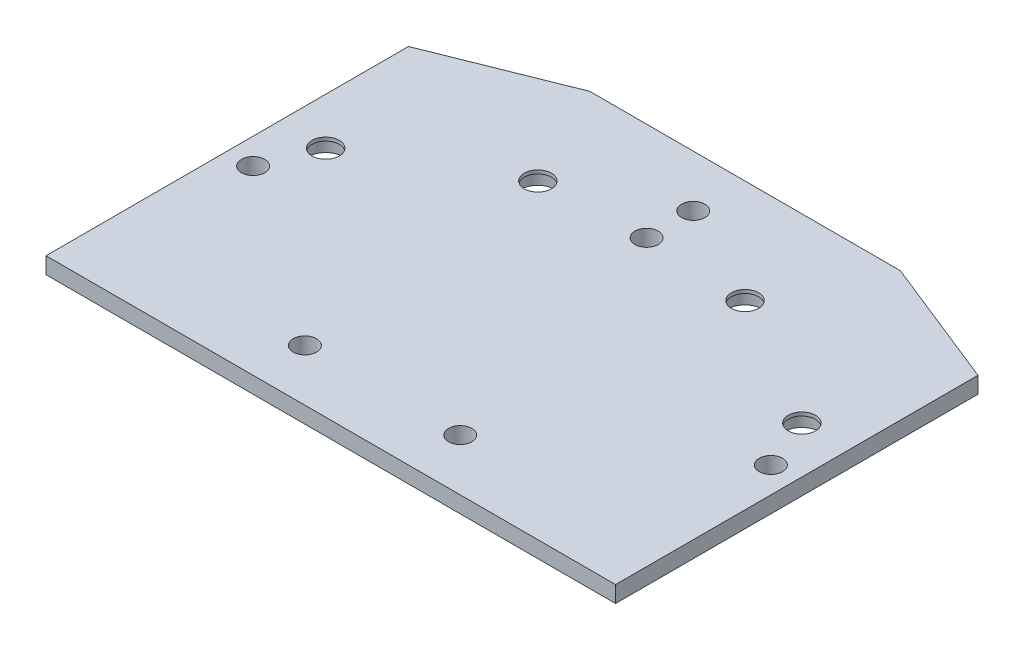
SolidWorks part; units mm, degrees
material "6061-T6 (SS)"
ref_plane "Front Plane" through (0, 0, 0) normal (0, 0, 1) x (1, 0, 0)
ref_plane "Top Plane" through (0, 0, 0) normal (0, 1, 0) x (1, 0, 0)
ref_plane "Right Plane" through (0, 0, 0) normal (1, 0, 0) x (0, 0, -1)
sketch "Sketch1" plane through (0, 0, 0) normal (0, 1, 0) x (1, 0, 0)
  line L0 (-55, 15) -> (-30, 25)
  line L1 (55, -55) -> (-55, -55)
  line L7 (30, 25) -> (55, 15)
  line L8 (-55, -55) -> (-55, 15)
  line L9 (55, -55) -> (55, 15)
  line L10 (30, 25) -> (-30, 25)
  point P0 (0, 0)
  dimension "D1" = 25
  dimension "D2" = 10
  dimension "D3" = 25
  dimension "D4" = 110
  dimension "D5" = 70
  dimension "D6" = 15
  dimension "D7" = 55
extrude "Boss-Extrude1" add sketch "Sketch1" along normal mid plane 3.175 contours L0 L10 L7 L9 L1 L8
sketch "Sketch4" plane through (0, 1.5875, 0) normal (0, 1, 0) x (1, 0, 0)
  line L0 (30, 25) -> (-30, 25) construction
  line L3 (-45.9808, -10) -> (-20, 5)
  line L5 (-55, -55) -> (-55, 15) construction
  point P0 (-20, 5)
  point P2 (20, 5)
  point P4 (45.9808, -10)
  point P6 (-45.9808, -10)
  dimension "D1" = 20
  dimension "D2" = 30
  dimension "D3" = 20
  dimension "D4" = 20
  dimension "D5" = 30
  dimension "D7" = 60
hole_wizard "Ø1.0mm Dowel Hole1" positions "Sketch4" profile "Sketch3" hole size "Ø1.0" standard "ANSI Metric" end condition through all
sketch "Sketch3" plane through (-20, 1.5875, -5) normal (1, 0, 0) x (0, 0, 1)
  line L0 (0, 0) -> (0, 3.175)
  line L1 (0, 3.175) -> (2.625, 3.175)
  line L2 (2.625, 3.175) -> (2.625, 0)
  line L5 (2.625, 0) -> (0, 0)
  line L11 (0, -6.35) -> (0, 107.95) construction
  dimension "Thru Hole Dia." = 5.25
  dimension "Thru Hole Depth" = 3.175
sketch "Sketch6" plane through (0, -1.5875, 0) normal (0, -1, 0) x (1, 0, 0)
  circle A0 centre (-45.9808, 10) radius 3.45
  circle A1 centre (-20, -5) radius 3.45
  circle A2 centre (20, -5) radius 3.45
  circle A3 centre (45.9808, 10) radius 3.45
  dimension "D1" = 6.9
  dimension "D2" = 6.9
  dimension "D3" = 6.9
  dimension "D4" = 6.9
extrude "Cut-Extrude2" cut sketch "Sketch6" against normal blind 2.5
sketch "Sketch9" plane through (0, -1.5875, 0) normal (0, -1, 0) x (-1, 0, 0)
  line L0 (-30, 25) -> (30, 25) construction
  point P0 (0, 15)
  point P2 (0, 6)
  point P5 (0, 0)
  dimension "D1" = 9
  dimension "D2" = 10
hole_wizard "M4 Clearance Hole1" positions "Sketch9" profile "Sketch8" hole size "M4" standard "ANSI Metric" end condition through all
sketch "Sketch8" plane through (0, -1.5875, -15) normal (1, 0, 0) x (0, 0, -1)
  line L0 (0, 0) -> (0, 3.175)
  line L1 (0, 3.175) -> (2.25, 3.175)
  line L2 (2.25, 3.175) -> (2.25, 0)
  line L5 (2.25, 0) -> (0, 0)
  line L11 (0, -6.35) -> (0, 107.95) construction
  dimension "Thru Hole Dia." = 4.5
  dimension "Thru Hole Depth" = 3.175
sketch "Sketch12" plane through (0, 1.5875, 0) normal (0, 1, 0) x (1, 0, 0)
  line L0 (55, -55) -> (-55, -55) construction
  point P0 (-15, -45)
  point P2 (15, -45)
  dimension "D1" = 15
  dimension "D2" = 30
  dimension "D3" = 10
hole_wizard "M4 Clearance Hole2" positions "Sketch12" profile "Sketch11" hole size "M4" standard "ANSI Metric" end condition through all
sketch "Sketch11" plane through (-15, 1.5875, 45) normal (1, 0, 0) x (0, 0, 1)
  line L0 (0, 0) -> (0, 3.175)
  line L1 (0, 3.175) -> (2.25, 3.175)
  line L2 (2.25, 3.175) -> (2.25, 0)
  line L5 (2.25, 0) -> (0, 0)
  line L11 (0, -6.35) -> (0, 107.95) construction
  dimension "Thru Hole Dia." = 4.5
  dimension "Thru Hole Depth" = 3.175
sketch "Sketch15" plane through (0, 1.5875, 0) normal (0, 1, 0) x (1, 0, 0)
  line L0 (-55, -55) -> (-55, 15) construction
  line L1 (55, -55) -> (55, 15) construction
  line L2 (55, -55) -> (-55, -55) construction
  point P0 (-50, -20)
  point P2 (50, -20)
  point P5 (0, 0)
  dimension "D1" = 5
  dimension "D2" = 5
  dimension "D3" = 35
hole_wizard "M4 Clearance Hole3" positions "Sketch15" profile "Sketch14" hole size "M4" standard "ANSI Metric" end condition through all
sketch "Sketch14" plane through (-50, 1.5875, 20) normal (1, 0, 0) x (0, 0, 1)
  line L0 (0, 0) -> (0, 3.175)
  line L1 (0, 3.175) -> (2.25, 3.175)
  line L2 (2.25, 3.175) -> (2.25, 0)
  line L5 (2.25, 0) -> (0, 0)
  line L11 (0, -6.35) -> (0, 107.95) construction
  dimension "Thru Hole Dia." = 4.5
  dimension "Thru Hole Depth" = 3.175
